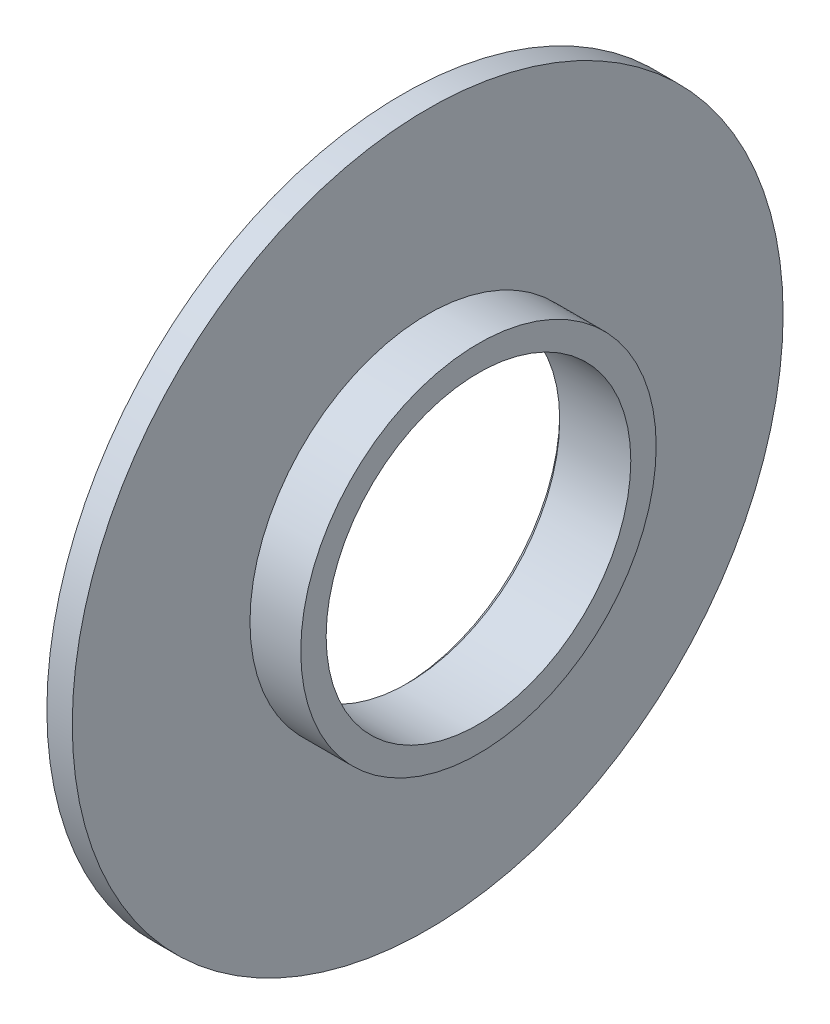
SolidWorks part; units mm, degrees
material "Alloy Steel (SS)"
ref_plane "Front Plane" through (0, 0, 0) normal (0, 0, 1) x (1, 0, 0)
ref_plane "Top Plane" through (0, 0, 0) normal (0, 1, 0) x (1, 0, 0)
ref_plane "Right Plane" through (0, 0, 0) normal (1, 0, 0) x (0, 0, -1)
sketch "Sketch1" plane through (0, 0, 0) normal (0, 0, 1) x (1, 0, 0)
  line L0 (0, 0) -> (3, 0) construction
  line L1 (0, 0) -> (0, 6) construction
  line L2 (0, 14) -> (0, 6)
  line L3 (0, 6) -> (3, 6)
  line L4 (3, 6) -> (3, 7)
  line L5 (3, 7) -> (1, 7)
  line L6 (1, 7) -> (1, 14)
  line L7 (1, 14) -> (0, 14)
  dimension "D1" = 3
  dimension "D2" = 6
  dimension "D3" = 1
  dimension "D4" = 1
  dimension "D5" = 8
  dimension "D6" = 3
revolve "Revolve1" add sketch "Sketch1" angle 360 about L0
chamfer "Chamfer1" distance 0.2 angle 45 1 edges at (0, 0, 6)
